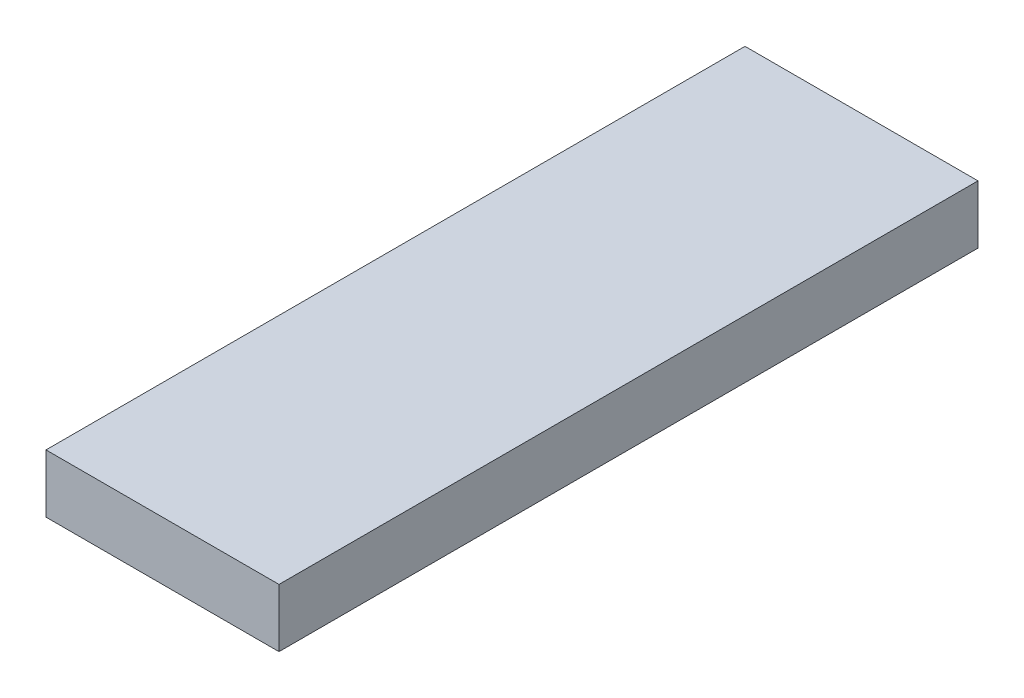
SolidWorks part; units mm, degrees
ref_plane "Front Plane" through (0, 0, 0) normal (0, 0, 1) x (1, 0, 0)
ref_plane "Top Plane" through (0, 0, 0) normal (0, 1, 0) x (1, 0, 0)
ref_plane "Right Plane" through (0, 0, 0) normal (1, 0, 0) x (0, 0, -1)
sketch "Sketch1" plane through (0, 0, 0) normal (0, 0, 1) x (1, 0, 0)
  line L1 (-10, -2.5) -> (10, -2.5)
  line L2 (-10, -2.5) -> (-10, 2.5)
  line L3 (-10, 2.5) -> (10, 2.5)
  line L4 (10, -2.5) -> (10, 2.5)
  line L5 (-10, -2.5) -> (10, 2.5) construction
  line L6 (-10, 2.5) -> (10, -2.5) construction
  point P0 (0, 0)
  dimension "D1" = 20
  dimension "D2" = 5
extrude "Link" add sketch "Sketch1" along normal mid plane 60
sketch "Hinges" plane through (0, 0, 0) normal (0, 0, 1) x (1, 0, 0)
  line L0 (0, -2.75) -> (0, 2.75) construction
  circle A0 centre (-10, -2.5) radius 1.5
  circle A1 centre (10, -2.5) radius 1.5
  dimension "D1" = 3
